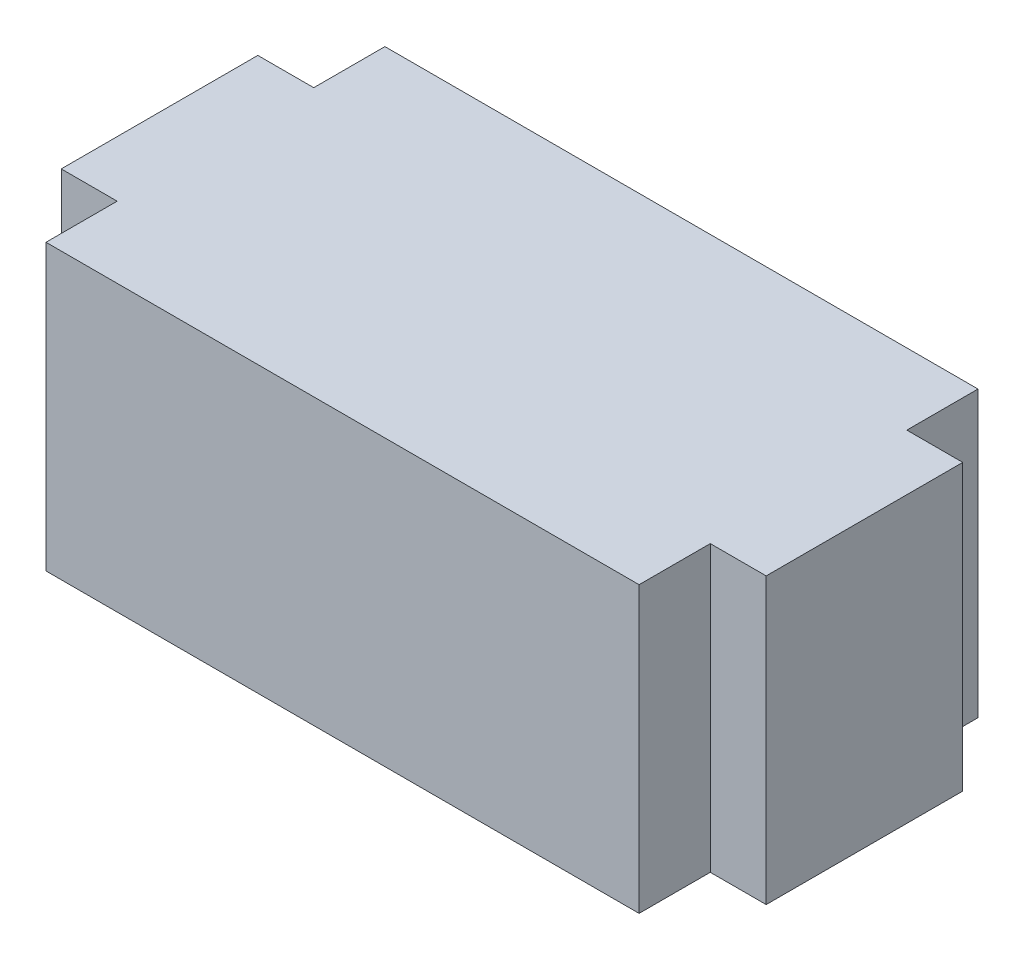
SolidWorks part; units mm, degrees
ref_plane "Front Plane" through (0, 0, 0) normal (0, 0, 1) x (1, 0, 0)
ref_plane "Top Plane" through (0, 0, 0) normal (0, 1, 0) x (1, 0, 0)
ref_plane "Right Plane" through (0, 0, 0) normal (1, 0, 0) x (0, 0, -1)
sketch "Sketch1" plane through (0, 0, 0) normal (0, 0, 1) x (1, 0, 0)
  line L1 (0, 0) -> (5.2, 0)
  line L2 (0, 0) -> (0, 2.1)
  line L3 (0, 2.1) -> (5.2, 2.1)
  line L4 (5.2, 0) -> (5.2, 2.1)
  dimension "D1" = 2.1
  dimension "D2" = 5.2
extrude "Boss-Extrude1" add sketch "Sketch1" along normal blind 2.5
sketch "Sketch2" plane through (0, 2.1, 0) normal (0, 1, 0) x (1, 0, 0)
  line L0 (2.6, 0) -> (2.6, -2.5) construction
  line L1 (5.2, 0) -> (0, 0) construction
  line L2 (5.2, -2.5) -> (0, -2.5) construction
  line L3 (0, -1.25) -> (5.2, -1.25) construction
  line L4 (0, -2.5) -> (0, 0) construction
  line L5 (5.2, -2.5) -> (5.2, 0) construction
  line L6 (4.7875, 0) -> (4.7875, -0.525)
  line L7 (0, 0) -> (0.4125, 0)
  line L8 (0, 0) -> (0, -0.525)
  line L9 (0, -0.525) -> (0.4125, -0.525)
  line L10 (0.4125, 0) -> (0.4125, -0.525)
  line L11 (5.2, -0.525) -> (4.7875, -0.525)
  line L12 (5.2, 0) -> (5.2, -0.525)
  line L13 (5.2, 0) -> (4.7875, 0)
  line L14 (5.2, -1.975) -> (4.7875, -1.975)
  line L15 (5.2, -2.5) -> (5.2, -1.975)
  line L16 (5.2, -2.5) -> (4.7875, -2.5)
  line L17 (4.7875, -2.5) -> (4.7875, -1.975)
  line L18 (0, -1.975) -> (0.4125, -1.975)
  line L19 (0, -2.5) -> (0, -1.975)
  line L20 (0, -2.5) -> (0.4125, -2.5)
  line L21 (0.4125, -2.5) -> (0.4125, -1.975)
  point P12 (2.6, -1.25)
  dimension "D1" = 0.4125
  dimension "D2" = 0.525
extrude "Cut-Extrude1" cut sketch "Sketch2" against normal through all
